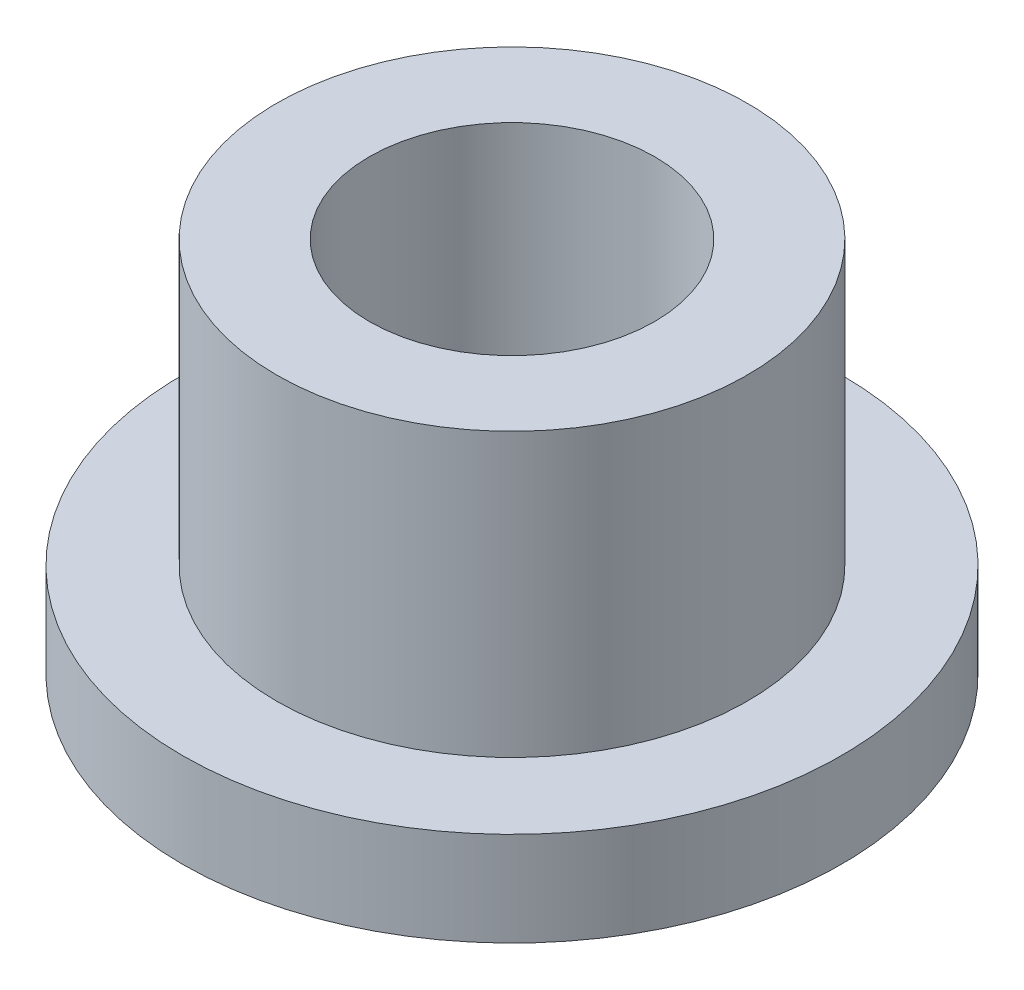
SolidWorks part; units mm, degrees
material "Rulon LR"
ref_plane "Front" through (0, 0, 0) normal (0, 0, 1) x (1, 0, 0)
ref_plane "Top" through (0, 0, 0) normal (0, 1, 0) x (1, 0, 0)
ref_plane "Right" through (0, 0, 0) normal (1, 0, 0) x (0, 0, -1)
sketch "Sketch1" plane through (0, 0, 0) normal (0, 1, 0) x (1, 0, 0)
  circle A0 centre (0, 0) radius 4.8133
  circle A1 centre (0, 0) radius 7.9375
  circle A2 centre (0, 0) radius 11.1125
  dimension "ID" = 9.6266
  dimension "OD" = 15.875
  dimension "FlangeOD" = 22.225
sketch "Sketch2" plane through (0, 0, 0) normal (0, 1, 0) x (1, 0, 0)
  circle A0 centre (0, 0) radius 4.8133 construction
  circle A1 centre (0, 0) radius 7.9375 construction
  circle A2 centre (0, 0) radius 4.8133
  circle A3 centre (0, 0) radius 7.9375
extrude "Boss-Extrude1" add sketch "Sketch2" along normal blind 12.7
sketch "Sketch3" plane through (0, 0, 0) normal (0, 1, 0) x (1, 0, 0)
  circle A0 centre (0, 0) radius 11.1125 construction
  circle A1 centre (0, 0) radius 7.9375 construction
  circle A2 centre (0, 0) radius 11.1125
  circle A3 centre (0, 0) radius 7.9375
extrude "Boss-Extrude2" add sketch "Sketch3" along normal blind 3.175
